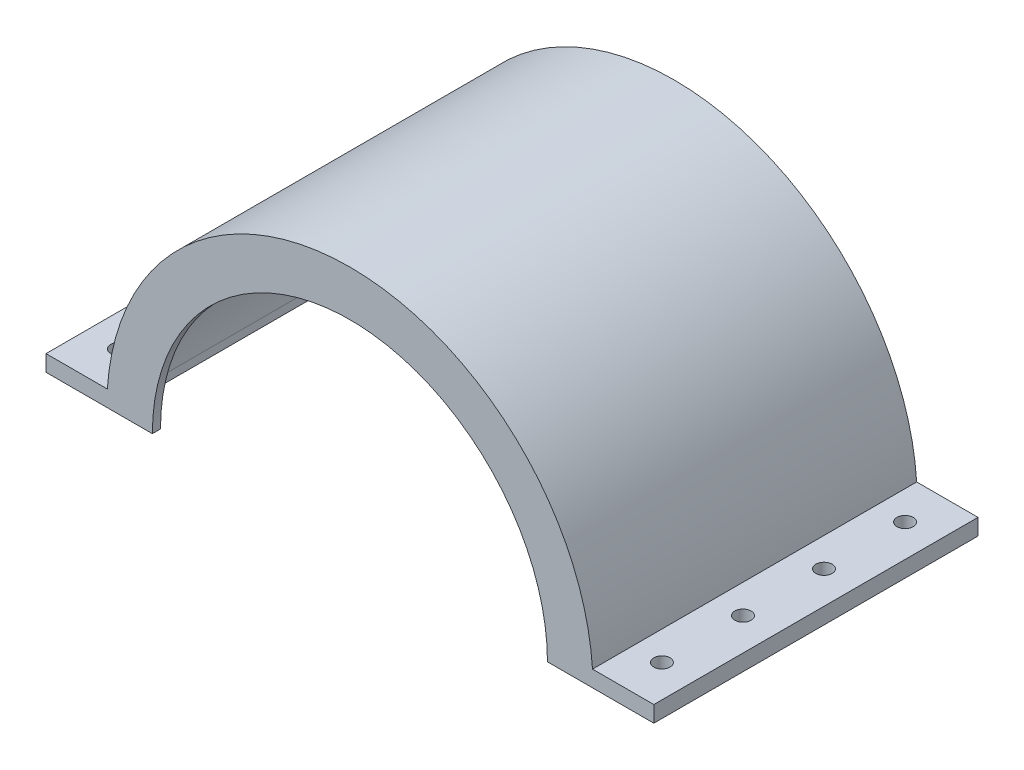
SolidWorks part; units mm, degrees
ref_plane "Front Plane" through (0, 0, 0) normal (0, 0, 1) x (1, 0, 0)
ref_plane "Top Plane" through (0, 0, 0) normal (0, 1, 0) x (1, 0, 0)
ref_plane "Right Plane" through (0, 0, 0) normal (1, 0, 0) x (0, 0, -1)
sketch "Sketch1" plane through (0, 0, 0) normal (0, 0, 1) x (1, 0, 0)
  line L0 (-75, 0) -> (75, 0)
  line L1 (0, 0) -> (0, 73.1042) construction
  line L2 (75, 0) -> (75, 4)
  line L3 (-75, 0) -> (-75, 4)
  line L4 (75, 4) -> (59.8665, 4)
  line L5 (-75, 4) -> (-59.8665, 4)
  arc A0 (59.8665, 4) -> (-59.8665, 4) centre (0, 0) ccw
  dimension "D1" = 120
  dimension "D2" = 75
  dimension "D3" = 73.1042
  dimension "D4" = 4
  dimension "D5" = 15.1335
extrude "Boss-Extrude1" add sketch "Sketch1" along normal blind 80
shell "Shell1" thickness 2
sketch "Sketch2" plane through (0, 2, 0) normal (0, -1, 0) x (1, 0, 0)
  line L1 (-73, 78) -> (-57.9655, 78)
  line L2 (-73, 78) -> (-73, 2)
  line L3 (-73, 2) -> (-57.9655, 2)
  line L4 (-57.9655, 78) -> (-57.9655, 2)
  line L5 (57.9123, 78) -> (73, 78)
  line L6 (57.9123, 78) -> (57.9123, 2)
  line L7 (57.9123, 2) -> (73, 2)
  line L8 (73, 78) -> (73, 2)
  dimension "D1" = 76
  dimension "D2" = 15.0345
  dimension "D3" = 76
  dimension "D4" = 15.0877
extrude "Boss-Extrude2" add sketch "Sketch2" along normal up to surface (2 mm away) up to face at (0, 0, 40)
sketch "Sketch3" plane through (0, 0, 80) normal (0, 0, 1) x (1, 0, 0)
  line L0 (-48.75, 0) -> (48.75, 0)
  arc A0 (48.75, 0) -> (-48.75, 0) centre (0, 0) ccw
  dimension "D2" = 97.5
extrude "Cut-Extrude1" cut sketch "Sketch3" against normal up to next
sketch "Sketch5" plane through (0, 0, 0) normal (0, 0, -1) x (-1, 0, 0)
  line L0 (-15, 0) -> (15, 0)
  arc A0 (15, 0) -> (-15, 0) centre (0, 0) ccw
  dimension "D1" = 30
  dimension "D2" = 30
extrude "Cut-Extrude2" cut sketch "Sketch5" against normal up to next
sketch "Sketch6" plane through (0, 0, 0) normal (0, -1, 0) x (1, 0, 0)
  circle A0 centre (67, 70) radius 2
  dimension "D3" = 4
  dimension "D4" = 67
  dimension "D5" = 70
extrude "Cut-Extrude6" cut sketch "Sketch6" against normal through all
pattern_linear "LPattern1" count 4 spacing 20 along (0, 0, -1) of "Cut-Extrude6"
ref_plane "Plane1" through (0, 0, 0) normal (1, 0, 0) x (0, 0, -1)
mirror "Mirror1" about plane through (0, 0, 0) normal (1, 0, 0) of "LPattern1", "Cut-Extrude6"
ref_plane "Plane2" through (-81.5, 0, 0) normal (1, 0, 0) x (0, 0, -1)
sketch "Sketch8" plane through (-81.5, 0, 0) normal (1, 0, 0) x (0, 0, -1)
  line L2 (-53.75, 97.3333) -> (-26.25, 97.3333)
  line L3 (-11.25, 82.3333) -> (-11.25, 70.3333)
  line L4 (-68.75, 82.3333) -> (-68.75, 70.3333)
  line L5 (-26.25, 55.3333) -> (-53.75, 55.3333)
  arc A0 (-11.25, 82.3333) -> (-26.25, 97.3333) centre (-26.25, 82.3333) ccw
  arc A1 (-26.25, 55.3333) -> (-11.25, 70.3333) centre (-26.25, 70.3333) ccw
  arc A2 (-68.75, 82.3333) -> (-53.75, 97.3333) centre (-53.75, 82.3333) cw
  arc A3 (-53.75, 55.3333) -> (-68.75, 70.3333) centre (-53.75, 70.3333) cw
  point P9 (-40, 55.3333)
  dimension "D1" = 15
  dimension "D2" = 15
  dimension "D3" = 15
  dimension "D4" = 15
  dimension "D5" = 55.3333
  dimension "D6" = 97.3333
  dimension "D7" = 40
  dimension "D8" = 27.5
ref_plane "Plane3" through (0, 0, 40) normal (0, 0, 1) x (1, 0, 0)
sketch "Sketch10" plane through (0, 0, 40) normal (0, 0, 1) x (1, 0, 0)
  line L0 (59.8665, 4) -> (-39.911, -2.6667) construction
  line L1 (-39.911, -2.6667) -> (-39.911, 97.3333) construction
  line L2 (-39.911, 97.3333) -> (-81.5, 97.3333)
  line L3 (-81.5, 82.3333) -> (-81.5, 97.3333) construction
  line L4 (-81.5, -45.1099) -> (-81.5, 45.1099) construction
  arc A0 (59.8665, 4) -> (-39.911, 97.3333) centre (-39.911, -2.6667) ccw
  dimension "D1" = 97.3333
  dimension "D2" = 39.911
sketch "Sketch11" plane through (0, 0, 40) normal (0, 0, 1) x (1, 0, 0)
  line L0 (-17.3845, 55.3333) -> (-81.5, 55.3333)
  line L2 (0, 0) -> (57.871, 3.8667) construction
  line L3 (59.8665, 4) -> (-39.911, -2.6667) construction
  arc A0 (57.871, 3.8667) -> (-17.3845, 55.3333) centre (0, 0) ccw
  point P0 (0, 0)
  dimension "D1" = 57.871
